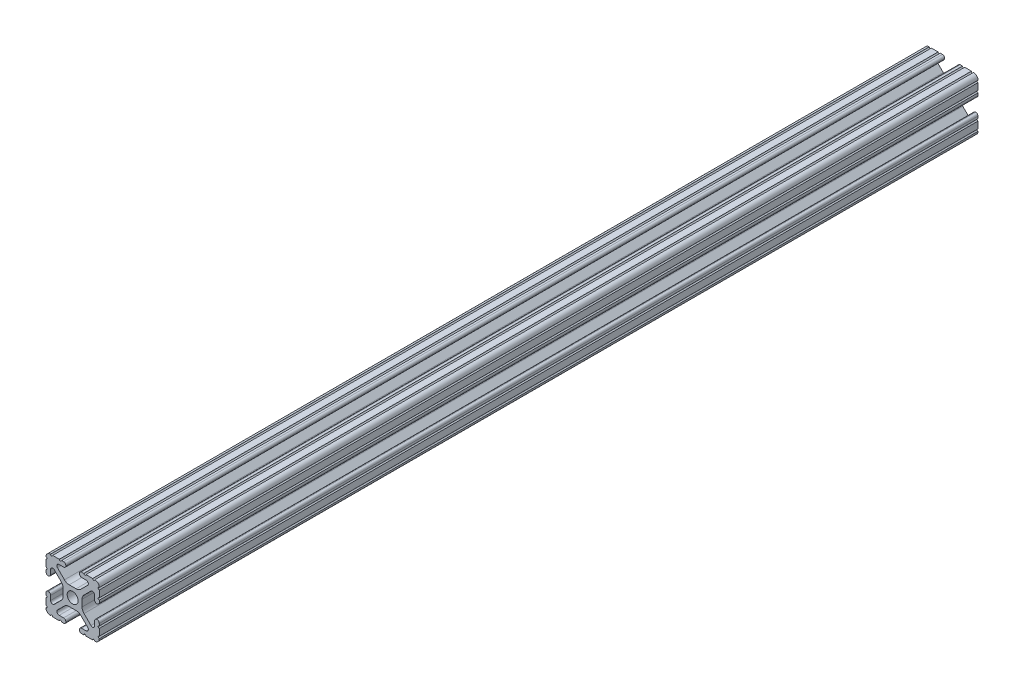
SolidWorks part; units mm, degrees
material "McMaster 6105-T5"
ref_plane "Front Plane" through (0, 0, 0) normal (0, 0, 1) x (1, 0, 0)
ref_plane "Top Plane" through (0, 0, 0) normal (0, 1, 0) x (1, 0, 0)
ref_plane "Right Plane" through (0, 0, 0) normal (1, 0, 0) x (0, 0, -1)
sketch "Sketch1" plane through (0, 0, 0) normal (0, 0, 1) x (1, 0, 0)
  line L88 (-7.1797, -8.6452) -> (-3.9523, -5.4237)
  line L89 (-1.7093, -4.4958) -> (1.7093, -4.4958)
  line L90 (3.9523, -5.4237) -> (7.1797, -8.6452)
  line L91 (6.4164, -10.4902) -> (4.2875, -10.4902)
  line L92 (3.2385, -11.5392) -> (3.2385, -11.651)
  line L93 (4.2875, -12.7) -> (5.3171, -12.7)
  line L94 (6.3331, -12.7) -> (9.5504, -12.7)
  line L95 (12.7, -9.5504) -> (12.7, -6.3331)
  line L96 (12.7, -5.3171) -> (12.7, -4.2875)
  line L97 (11.651, -3.2385) -> (11.5392, -3.2385)
  line L98 (10.4902, -4.2875) -> (10.4902, -6.4021)
  line L99 (8.7371, -7.1294) -> (5.441, -3.8408)
  line L100 (4.5085, -1.5932) -> (4.5085, 1.5932)
  line L101 (5.441, 3.8408) -> (8.7371, 7.1294)
  line L102 (10.4902, 6.4021) -> (10.4902, 4.2875)
  line L103 (11.5392, 3.2385) -> (11.651, 3.2385)
  line L104 (12.7, 4.2875) -> (12.7, 5.3171)
  line L105 (12.7, 6.3331) -> (12.7, 9.5504)
  line L106 (9.5504, 12.7) -> (6.3331, 12.7)
  line L107 (5.3171, 12.7) -> (4.2875, 12.7)
  line L108 (3.2385, 11.651) -> (3.2385, 11.5392)
  line L109 (4.2875, 10.4902) -> (6.4768, 10.4902)
  line L110 (7.207, 8.7244) -> (3.8983, 5.4232)
  line L111 (1.6558, 4.4958) -> (-1.6558, 4.4958)
  line L112 (-3.8983, 5.4232) -> (-7.207, 8.7244)
  line L113 (-6.4768, 10.4902) -> (-4.2875, 10.4902)
  line L114 (-3.2385, 11.5392) -> (-3.2385, 11.651)
  line L115 (-4.2875, 12.7) -> (-5.3171, 12.7)
  line L116 (-6.3331, 12.7) -> (-9.5504, 12.7)
  line L117 (-12.7, 9.5504) -> (-12.7, 6.3331)
  line L118 (-12.7, 5.3171) -> (-12.7, 4.2875)
  line L119 (-11.651, 3.2385) -> (-11.5392, 3.2385)
  line L120 (-10.4902, 4.2875) -> (-10.4902, 6.4021)
  line L121 (-8.7371, 7.1294) -> (-5.441, 3.8408)
  line L122 (-4.5085, 1.5932) -> (-4.5085, -1.5932)
  line L123 (-5.441, -3.8408) -> (-8.7371, -7.1294)
  line L124 (-10.4902, -6.4021) -> (-10.4902, -4.2875)
  line L125 (-11.5392, -3.2385) -> (-11.651, -3.2385)
  line L126 (-12.7, -4.2875) -> (-12.7, -5.3171)
  line L127 (-12.7, -6.3331) -> (-12.7, -9.5504)
  line L128 (-9.5504, -12.7) -> (-6.3331, -12.7)
  line L129 (-5.3171, -12.7) -> (-4.2875, -12.7)
  line L130 (-3.2385, -11.651) -> (-3.2385, -11.5392)
  line L131 (-4.2875, -10.4902) -> (-6.4164, -10.4902)
  circle A1 centre (0, 0) radius 2.6035
  arc A104 (-7.1797, -8.6452) -> (-6.4164, -10.4902) centre (-6.4164, -9.4098) ccw
  arc A105 (-1.7093, -4.4958) -> (-3.9523, -5.4237) centre (-1.7093, -7.6708) ccw
  arc A106 (3.9523, -5.4237) -> (1.7093, -4.4958) centre (1.7093, -7.6708) ccw
  arc A107 (6.4164, -10.4902) -> (7.1797, -8.6452) centre (6.4164, -9.4098) ccw
  arc A108 (4.2875, -10.4902) -> (3.2385, -11.5392) centre (4.2875, -11.5392) ccw
  arc A109 (3.2385, -11.651) -> (4.2875, -12.7) centre (4.2875, -11.651) ccw
  arc A110 (6.3331, -12.7) -> (5.3171, -12.7) centre (5.8251, -12.7) ccw
  arc A111 (10.5664, -12.6998) -> (9.5504, -12.7) centre (10.0584, -12.7) ccw
  arc A112 (10.5664, -12.6998) -> (12.6998, -10.5664) centre (10.5918, -10.5918) ccw
  arc A113 (12.7, -9.5504) -> (12.6998, -10.5664) centre (12.7, -10.0584) ccw
  arc A114 (12.7, -5.3171) -> (12.7, -6.3331) centre (12.7, -5.8251) ccw
  arc A115 (12.7, -4.2875) -> (11.651, -3.2385) centre (11.651, -4.2875) ccw
  arc A116 (11.5392, -3.2385) -> (10.4902, -4.2875) centre (11.5392, -4.2875) ccw
  arc A117 (8.7371, -7.1294) -> (10.4902, -6.4021) centre (9.4628, -6.4021) ccw
  arc A118 (4.5085, -1.5932) -> (5.441, -3.8408) centre (7.6835, -1.5932) ccw
  arc A119 (5.441, 3.8408) -> (4.5085, 1.5932) centre (7.6835, 1.5932) ccw
  arc A120 (10.4902, 6.4021) -> (8.7371, 7.1294) centre (9.4628, 6.4021) ccw
  arc A121 (10.4902, 4.2875) -> (11.5392, 3.2385) centre (11.5392, 4.2875) ccw
  arc A122 (11.651, 3.2385) -> (12.7, 4.2875) centre (11.651, 4.2875) ccw
  arc A123 (12.7, 6.3331) -> (12.7, 5.3171) centre (12.7, 5.8251) ccw
  arc A124 (12.6998, 10.5664) -> (12.7, 9.5504) centre (12.7, 10.0584) ccw
  arc A125 (12.6998, 10.5664) -> (10.5664, 12.6998) centre (10.5918, 10.5918) ccw
  arc A126 (9.5504, 12.7) -> (10.5664, 12.6998) centre (10.0584, 12.7) ccw
  arc A127 (5.3171, 12.7) -> (6.3331, 12.7) centre (5.8251, 12.7) ccw
  arc A128 (4.2875, 12.7) -> (3.2385, 11.651) centre (4.2875, 11.651) ccw
  arc A129 (3.2385, 11.5392) -> (4.2875, 10.4902) centre (4.2875, 11.5392) ccw
  arc A130 (7.207, 8.7244) -> (6.4768, 10.4902) centre (6.4768, 9.4563) ccw
  arc A131 (1.6558, 4.4958) -> (3.8983, 5.4232) centre (1.6558, 7.6708) ccw
  arc A132 (-3.8983, 5.4232) -> (-1.6558, 4.4958) centre (-1.6558, 7.6708) ccw
  arc A133 (-6.4768, 10.4902) -> (-7.207, 8.7244) centre (-6.4768, 9.4563) ccw
  arc A134 (-4.2875, 10.4902) -> (-3.2385, 11.5392) centre (-4.2875, 11.5392) ccw
  arc A135 (-3.2385, 11.651) -> (-4.2875, 12.7) centre (-4.2875, 11.651) ccw
  arc A136 (-6.3331, 12.7) -> (-5.3171, 12.7) centre (-5.8251, 12.7) ccw
  arc A137 (-10.5664, 12.6998) -> (-9.5504, 12.7) centre (-10.0584, 12.7) ccw
  arc A138 (-10.5664, 12.6998) -> (-12.6998, 10.5664) centre (-10.5918, 10.5918) ccw
  arc A139 (-12.7, 9.5504) -> (-12.6998, 10.5664) centre (-12.7, 10.0584) ccw
  arc A140 (-12.7, 5.3171) -> (-12.7, 6.3331) centre (-12.7, 5.8251) ccw
  arc A141 (-12.7, 4.2875) -> (-11.651, 3.2385) centre (-11.651, 4.2875) ccw
  arc A142 (-11.5392, 3.2385) -> (-10.4902, 4.2875) centre (-11.5392, 4.2875) ccw
  arc A143 (-8.7371, 7.1294) -> (-10.4902, 6.4021) centre (-9.4628, 6.4021) ccw
  arc A144 (-4.5085, 1.5932) -> (-5.441, 3.8408) centre (-7.6835, 1.5932) ccw
  arc A145 (-5.441, -3.8408) -> (-4.5085, -1.5932) centre (-7.6835, -1.5932) ccw
  arc A146 (-10.4902, -6.4021) -> (-8.7371, -7.1294) centre (-9.4628, -6.4021) ccw
  arc A147 (-10.4902, -4.2875) -> (-11.5392, -3.2385) centre (-11.5392, -4.2875) ccw
  arc A148 (-11.651, -3.2385) -> (-12.7, -4.2875) centre (-11.651, -4.2875) ccw
  arc A149 (-12.7, -6.3331) -> (-12.7, -5.3171) centre (-12.7, -5.8251) ccw
  arc A150 (-12.6998, -10.5664) -> (-12.7, -9.5504) centre (-12.7, -10.0584) ccw
  arc A151 (-12.6998, -10.5664) -> (-10.5664, -12.6998) centre (-10.5918, -10.5918) ccw
  arc A152 (-9.5504, -12.7) -> (-10.5664, -12.6998) centre (-10.0584, -12.7) ccw
  arc A153 (-5.3171, -12.7) -> (-6.3331, -12.7) centre (-5.8251, -12.7) ccw
  arc A154 (-4.2875, -12.7) -> (-3.2385, -11.651) centre (-4.2875, -11.651) ccw
  arc A155 (-3.2385, -11.5392) -> (-4.2875, -10.4902) centre (-4.2875, -11.5392) ccw
extrude "Boss-Extrude1" add sketch "Sketch1" along normal mid plane 419.1
sketch "Sketch2" plane through (0, 12.7, 0) normal (0, 1, 0) x (1, 0, 0)
  line L0 (0, -155.4789) -> (0, 151.1822) construction
  line L1 (1.6558, -209.55) -> (-1.6558, -209.55) construction
  line L2 (1.6558, 209.55) -> (-1.6558, 209.55) construction
  circle A0 centre (0, -146.05) radius 3.175
  circle A1 centre (0, 184.15) radius 3.175
  point P4 (0, -209.55)
  point P12 (0, 209.55)
  dimension "D3" = 6.35
  dimension "D1" = 63.5
  dimension "D2" = 25.4
extrude "Cut-Extrude1" [suppressed] cut sketch "Sketch2" against normal through all both and the other way through all
sketch "Sketch3" plane through (-12.7, 0, 0) normal (-1, 0, 0) x (0, 0, 1)
  line L0 (-144.1574, 0) -> (-126.6701, 0) construction
  line L2 (209.55, 1.5932) -> (209.55, -1.5932) construction
  line L3 (-209.55, 1.5932) -> (-209.55, -1.5932) construction
  circle A0 centre (-158.75, 0) radius 3.175
  circle A1 centre (-133.35, 0) radius 3.175
  dimension "D1" = 6.35
  dimension "D2" = 342.9
  dimension "D3" = 50.8
extrude "Cut-Extrude2" [suppressed] cut sketch "Sketch3" against normal through all both and the other way through all
sketch "Sketch4" plane through (0, 12.7, 0) normal (0, 1, 0) x (1, 0, 0)
  circle A0 centre (0, 346.7409) radius 3.175 construction
  circle A1 centre (0, -85.0591) radius 3.175 construction
  circle A2 centre (0, 346.7409) radius 3.175
  circle A3 centre (0, -85.0591) radius 3.175
extrude "Cut-Extrude3" cut sketch "Sketch4" against normal through all both and the other way through all
sketch "Sketch5" plane through (0, 4.4958, 0) normal (0, 1, 0) x (1, 0, 0)
  circle A0 centre (0, -52.2049) radius 6.35
  circle A1 centre (0, 323.1563) radius 6.35
  dimension "D1" = 12.7
extrude "Cut-Extrude4" [suppressed] cut sketch "Sketch5" along normal blind 12.7
